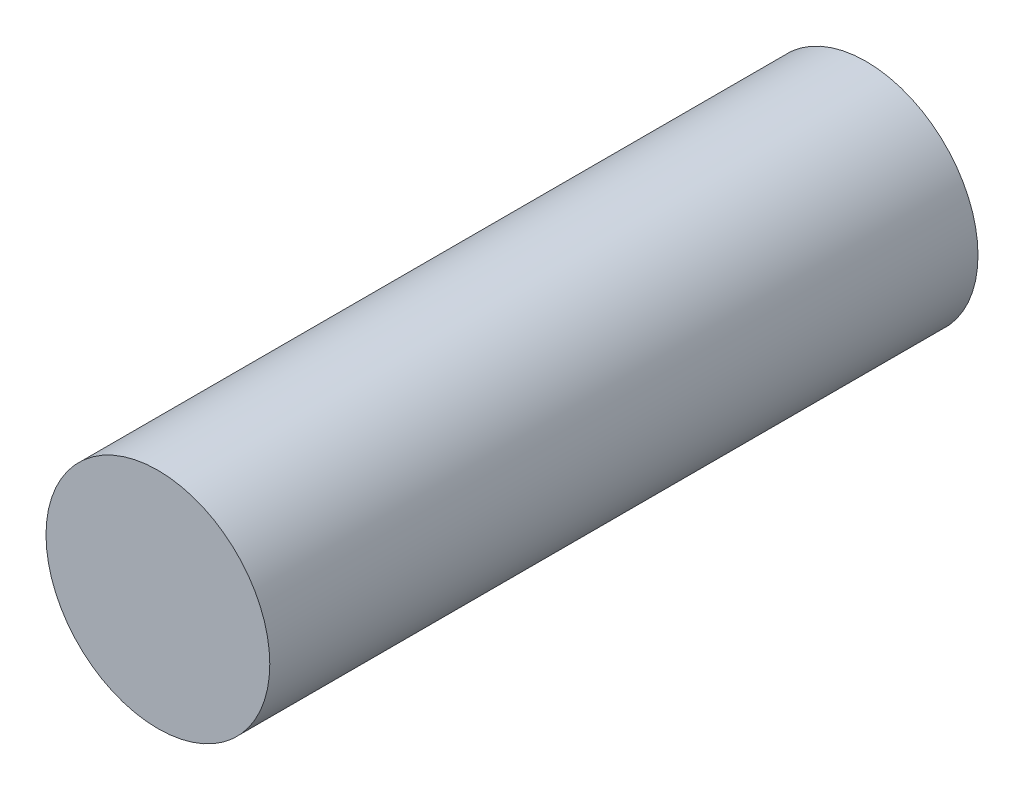
SolidWorks part; units mm, degrees
ref_plane "Front Plane" through (0, 0, 0) normal (0, 0, 1) x (1, 0, 0)
ref_plane "Top Plane" through (0, 0, 0) normal (0, 1, 0) x (1, 0, 0)
ref_plane "Right Plane" through (0, 0, 0) normal (1, 0, 0) x (0, 0, -1)
sketch "Sketch1" plane through (0, 0, 0) normal (0, 0, 1) x (1, 0, 0)
  circle A0 centre (0, 0) radius 7.9
  dimension "D1" = 15.8
extrude "Boss-Extrude1" add sketch "Sketch1" along normal blind 50
